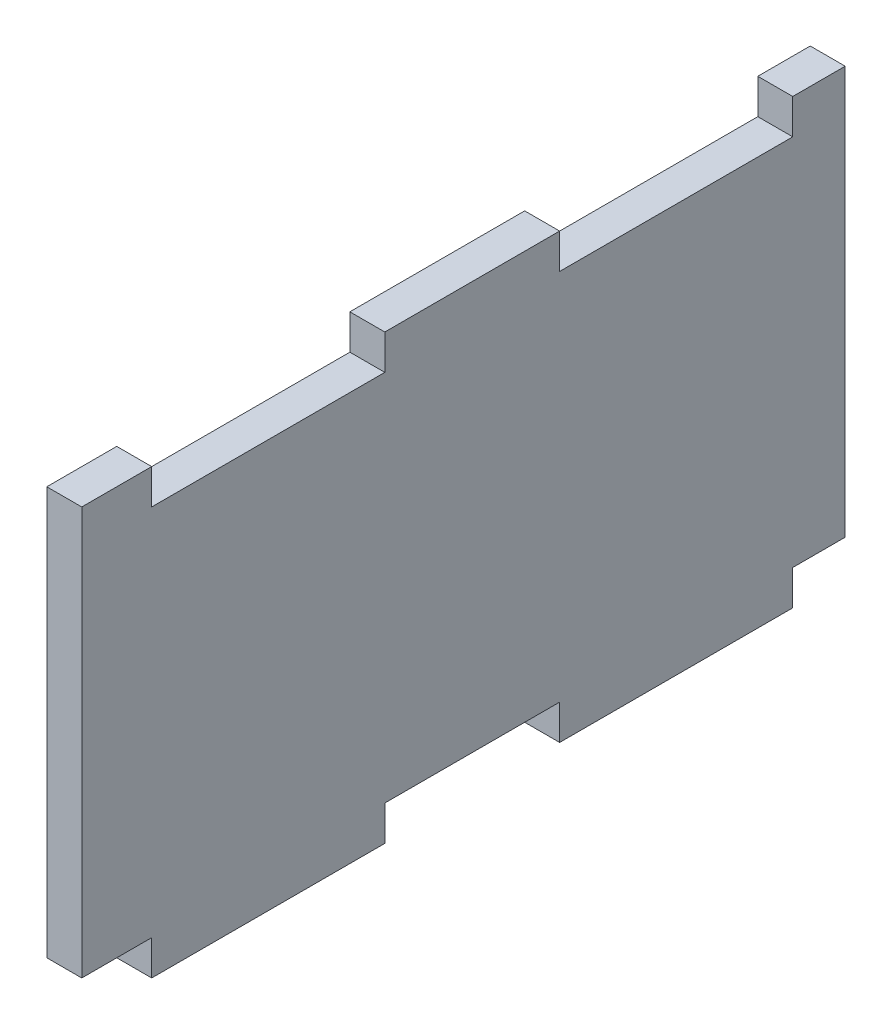
SolidWorks part; units mm, degrees
ref_plane "Front Plane" through (0, 0, 0) normal (0, 0, 1) x (1, 0, 0)
ref_plane "Top Plane" through (0, 0, 0) normal (0, 1, 0) x (1, 0, 0)
ref_plane "Right Plane" through (0, 0, 0) normal (1, 0, 0) x (0, 0, -1)
sketch "Sketch1" plane through (0, 0, 0) normal (1, 0, 0) x (0, 0, -1)
  line L0 (26, 0) -> (41, 0)
  line L1 (0, 0) -> (6, 0)
  line L2 (0, 0) -> (0, 35)
  line L3 (0, 35) -> (6, 35)
  line L4 (277, 0) -> (277, 35)
  line L5 (26, 35) -> (41, 35)
  line L6 (41, 32) -> (61, 32)
  line L7 (41, 0) -> (41, -3)
  line L8 (6, 0) -> (6, -3)
  line L9 (6, -3) -> (26, -3)
  line L10 (26, 0) -> (26, -3)
  line L11 (6, 35) -> (6, 32)
  line L12 (6, 32) -> (26, 32)
  line L13 (41, -3) -> (61, -3)
  line L14 (61, 0) -> (61, -3)
  line L15 (76, 0) -> (76, -3)
  line L16 (76, -3) -> (96, -3)
  line L17 (96, 0) -> (96, -3)
  line L18 (111, 0) -> (111, -3)
  line L19 (111, -3) -> (131, -3)
  line L20 (131, 0) -> (131, -3)
  line L21 (146, 0) -> (146, -3)
  line L22 (146, -3) -> (166, -3)
  line L23 (166, 0) -> (166, -3)
  line L24 (181, 0) -> (181, -3)
  line L25 (181, -3) -> (201, -3)
  line L26 (201, 0) -> (201, -3)
  line L27 (216, 0) -> (216, -3)
  line L28 (216, -3) -> (236, -3)
  line L29 (236, 0) -> (236, -3)
  line L30 (251, 0) -> (251, -3)
  line L31 (251, -3) -> (271, -3)
  line L32 (271, 0) -> (271, -3)
  line L33 (61, 0) -> (76, 0)
  line L34 (96, 0) -> (111, 0)
  line L35 (131, 0) -> (146, 0)
  line L36 (166, 0) -> (181, 0)
  line L37 (201, 0) -> (216, 0)
  line L38 (236, 0) -> (251, 0)
  line L39 (271, 0) -> (277, 0)
  line L40 (26, 35) -> (26, 32)
  line L41 (61, 35) -> (61, 32)
  line L42 (41, 35) -> (41, 32)
  line L43 (76, 32) -> (96, 32)
  line L44 (96, 35) -> (96, 32)
  line L45 (76, 35) -> (76, 32)
  line L46 (111, 32) -> (131, 32)
  line L47 (131, 35) -> (131, 32)
  line L48 (111, 35) -> (111, 32)
  line L49 (146, 32) -> (166, 32)
  line L50 (166, 35) -> (166, 32)
  line L51 (146, 35) -> (146, 32)
  line L52 (181, 32) -> (201, 32)
  line L53 (201, 35) -> (201, 32)
  line L54 (181, 35) -> (181, 32)
  line L55 (216, 32) -> (236, 32)
  line L56 (236, 35) -> (236, 32)
  line L57 (216, 35) -> (216, 32)
  line L58 (251, 32) -> (271, 32)
  line L59 (271, 35) -> (271, 32)
  line L60 (251, 35) -> (251, 32)
  line L61 (61, 35) -> (76, 35)
  line L62 (96, 35) -> (111, 35)
  line L63 (131, 35) -> (146, 35)
  line L64 (166, 35) -> (181, 35)
  line L65 (271, 35) -> (277, 35)
  line L66 (201, 35) -> (216, 35)
  line L67 (236, 35) -> (251, 35)
  dimension "D1" = 20
  dimension "D2" = 6
  dimension "D3" = 277
  dimension "D4" = 3
  dimension "D6" = 35
  dimension "D7" = 15
  dimension "D5" = 8
  dimension "D8" = 8
extrude "Boss-Extrude1" add sketch "Sketch1" along normal blind 3 contours L3 L11 L12 L40 L5 L42 L6 L41 L61 L45 L43 L44 L62 L48 L46 L47 L63 L51 L49 L50 L64 L54 L52 L53 L66 L57 L55 L56 L67 L60 L58 L59 L65 L4 L39 L32 L31 L30 L38 L29 L28 L27 L37 L26 L25 L24 L36 L23 L22 L21 L35 L20 L19 L18 L34 L17 L16 L15 L33 L14 L13 L7 L0 L10 L9 L8 L1 L2
sketch "Sketch2" plane through (3, 0, 0) normal (1, 0, 0) x (0, 0, -1)
  line L0 (0, 0) -> (0, 35) construction
  line L1 (65.5, 40) -> (277, 40)
  line L2 (65.5, 40) -> (65.5, -5)
  line L3 (65.5, -5) -> (277, -5)
  line L4 (277, 40) -> (277, -5)
  line L5 (65.5, 40) -> (277, -5) construction
  line L6 (65.5, -5) -> (277, 40) construction
  line L7 (277, 0) -> (277, 35) construction
  point P4 (171.25, 17.5)
  point P7 (65.5, 17.5)
  point P8 (0, 17.5)
  point P11 (277, 17.5)
  dimension "D1" = 65.5
  dimension "D2" = 45
extrude "Cut-Extrude1" cut sketch "Sketch2" against normal blind 10
